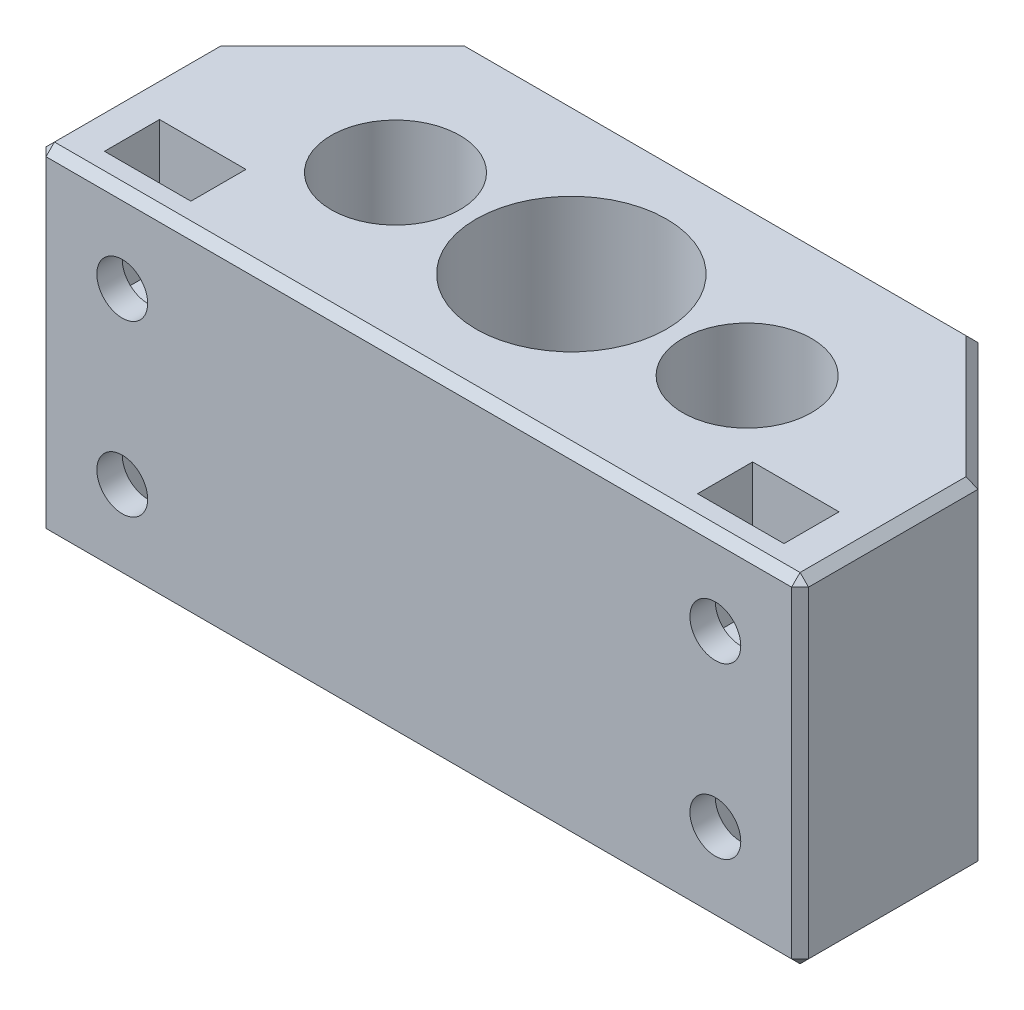
SolidWorks part; units mm, degrees
ref_plane "Front Plane" through (0, 0, 0) normal (0, 0, 1) x (1, 0, 0)
ref_plane "Top Plane" through (0, 0, 0) normal (0, 1, 0) x (1, 0, 0)
ref_plane "Right Plane" through (0, 0, 0) normal (1, 0, 0) x (0, 0, -1)
sketch "Sketch1" plane through (0, 0, 0) normal (0, 1, 0) x (1, 0, 0)
  line L0 (0, 0) -> (-20.75, 0) construction
  line L1 (0, 0) -> (0, 18) construction
  line L2 (0, 0) -> (0, -18) construction
  line L3 (0, 18) -> (-45, 18) construction
  line L5 (-45, 18) -> (45, 18)
  line L6 (-45, 18) -> (-45, -18)
  line L7 (-45, -18) -> (45, -18)
  line L8 (45, 18) -> (45, -18)
  circle A0 centre (0, 0) radius 5.25
  circle A1 centre (-20.75, 0) radius 7.6
  circle A2 centre (20.75, 0) radius 7.6
  dimension "D1" = 10.5
  dimension "D3" = 15.2
  dimension "D2" = 20.75
  dimension "D4" = 18
  dimension "D5" = 18
  dimension "D6" = 45
  dimension "D7" = 90
  dimension "D8" = 36
extrude "Boss-Extrude1" add sketch "Sketch1" against normal mid plane 40
sketch "Sketch2" plane through (0, 20, 0) normal (0, 1, 0) x (1, 0, 0)
  circle A0 centre (0, 0) radius 11.25
  dimension "D1" = 22.5
extrude "Cut-Extrude1" cut sketch "Sketch2" against normal blind 20
chamfer "Chamfer1" distance 15 angle 45 2 edges at (45, 0, -18) (-45, 0, -18)
sketch "Sketch4" plane through (0, 0, 0) normal (0, 1, 0) x (1, 0, 0)
  line L0 (0, 0) -> (0, 11.25) construction
  circle A0 centre (0, 0) radius 11.25 construction
  circle A1 centre (0, 0) radius 11.25 construction
  circle A2 centre (0, 8) radius 1.65
  circle A3 centre (8, 0) radius 1.65
  circle A4 centre (0, -8) radius 1.65
  circle A5 centre (-8, 0) radius 1.65
  point P18 (0, 0)
  dimension "D1" = 3.3
  dimension "D2" = 8
  dimension "D4" = 8
  dimension "D5" = 8
  dimension "D3" = 4
extrude "Cut-Extrude2" cut sketch "Sketch4" against normal up to next
sketch "Sketch11" plane through (0, -20, 0) normal (0, -1, 0) x (1, 0, 0)
  circle A0 centre (-8, 0) radius 2.65
  circle A1 centre (0, 8) radius 2.65
  circle A2 centre (8, 0) radius 2.65
  circle A3 centre (0, -8) radius 2.65
  point P12 (0, 0)
  dimension "D1" = 5.3
  dimension "D3" = 8
  dimension "D4" = 8
  dimension "D2" = 4
extrude "Cut-Extrude7" cut sketch "Sketch11" against normal blind 5.3
sketch "Sketch12" plane through (0, 0, 18) normal (0, 0, 1) x (1, 0, 0)
  line L0 (0, 20) -> (0, -20) construction
  line L1 (-45, 20) -> (45, 20) construction
  line L2 (-45, -20) -> (45, -20) construction
  circle A0 centre (-35, 10) radius 3
  circle A1 centre (-35, -10) radius 3
  circle A2 centre (35, -10) radius 3
  circle A3 centre (35, 10) radius 3
  dimension "D1" = 6
  dimension "D2" = 10
  dimension "D3" = 35
  dimension "D4" = 2
  dimension "D5" = 20
extrude "Cut-Extrude8" cut sketch "Sketch12" against normal blind 5
sketch "Sketch14" plane through (0, 0, 18) normal (0, 0, 1) x (1, 0, 0)
  line L11 (-45, 0) -> (45, 0) construction
  line L12 (-40.1, 4.75) -> (-29.9, 4.75)
  line L17 (0, 20) -> (0, -20) construction
  line L18 (-45, 20) -> (45, 20) construction
  line L19 (-45, -20) -> (45, -20) construction
  line L20 (-40.1, 4.75) -> (-40.1, 15.25)
  line L21 (-40.1, 15.25) -> (-29.9, 15.25)
  line L22 (-29.9, 4.75) -> (-29.9, 15.25)
  line L23 (-40.1, 4.75) -> (-29.9, 15.25) construction
  line L28 (-40.1, 15.25) -> (-29.9, 4.75) construction
  line L29 (-45, -20) -> (-45, 20) construction
  line L30 (45, -20) -> (45, 20) construction
  line L31 (-29.9, -15.25) -> (-29.9, -20)
  line L32 (-40.1, 15.25) -> (-29.9, 15.25)
  line L33 (-40.1, 15.25) -> (-40.1, 20)
  line L34 (-40.1, 20) -> (-29.9, 20)
  line L35 (-29.9, 15.25) -> (-29.9, 20)
  line L36 (-40.1, -20) -> (-29.9, -20)
  line L37 (-40.1, -15.25) -> (-40.1, -20)
  line L42 (-40.1, -15.25) -> (-29.9, -15.25)
  line L43 (-29.9, -4.75) -> (-29.9, -15.25)
  line L44 (-40.1, -15.25) -> (-29.9, -15.25)
  line L45 (-40.1, -4.75) -> (-40.1, -15.25)
  line L50 (-40.1, -4.75) -> (-29.9, -4.75)
  line L51 (40.1, -4.75) -> (29.9, -4.75)
  line L52 (40.1, -4.75) -> (40.1, -15.25)
  line L53 (40.1, -15.25) -> (29.9, -15.25)
  line L54 (29.9, -4.75) -> (29.9, -15.25)
  line L55 (40.1, -15.25) -> (29.9, -15.25)
  line L56 (40.1, -15.25) -> (40.1, -20)
  line L57 (40.1, -20) -> (29.9, -20)
  line L58 (29.9, -15.25) -> (29.9, -20)
  line L59 (40.1, 15.25) -> (29.9, 15.25)
  line L60 (29.9, 4.75) -> (29.9, 15.25)
  line L61 (40.1, 4.75) -> (29.9, 4.75)
  line L62 (40.1, 4.75) -> (40.1, 15.25)
  line L63 (40.1, 20) -> (29.9, 20)
  line L64 (29.9, 15.25) -> (29.9, 20)
  line L65 (40.1, 15.25) -> (29.9, 15.25)
  line L66 (40.1, 15.25) -> (40.1, 20)
  circle A0 centre (-35, -10) radius 3
  circle A1 centre (35, -10) radius 3
  circle A2 centre (35, 10) radius 3
  circle A3 centre (-35, 10) radius 3
  point P0 (-35, 10)
  circle M24 centre (35, 10) radius 3
  circle M25 centre (-35, -10) radius 3
  circle M26 centre (35, -10) radius 3
  circle M27 centre (-35, 10) radius 3
  line M28 (45, 20) -> (-45, 20)
  line M30 (-45, -20) -> (45, -20)
  dimension "D1" = 10.5
  dimension "D3" = 6
  dimension "D2" = 10.2
extrude "Cut-Extrude10" cut sketch "Sketch14" against normal blind 6.5 from offset 3 contours L21 L35 L33 M28 | L12 L22 L21 L20 M27 | L50 L45 L42 L43 M25 | L42 L37 L31 M30 | L51 L54 L53 L52 M26 | L53 L58 L56 M30 | L61 L62 L59 L60 M24 | L59 L66 L64 M28 | A0 | A1 | A2 offset against normal yes
chamfer "Chamfer2" distance 1 angle 45 14 edges at (-37.5, -20, -10.5) (0, -20, -18) (37.5, -20, -10.5) (37.5, 20, -10.5) (0, 20, -18) (-37.5, 20, -10.5) (45, -20, 7.5) (45, 20, 7.5) (45, 0, 18) (0, -20, 18) (-45, -20, 7.5) (-45, 0, 18) (0, 20, 18) (-45, 20, 7.5)
